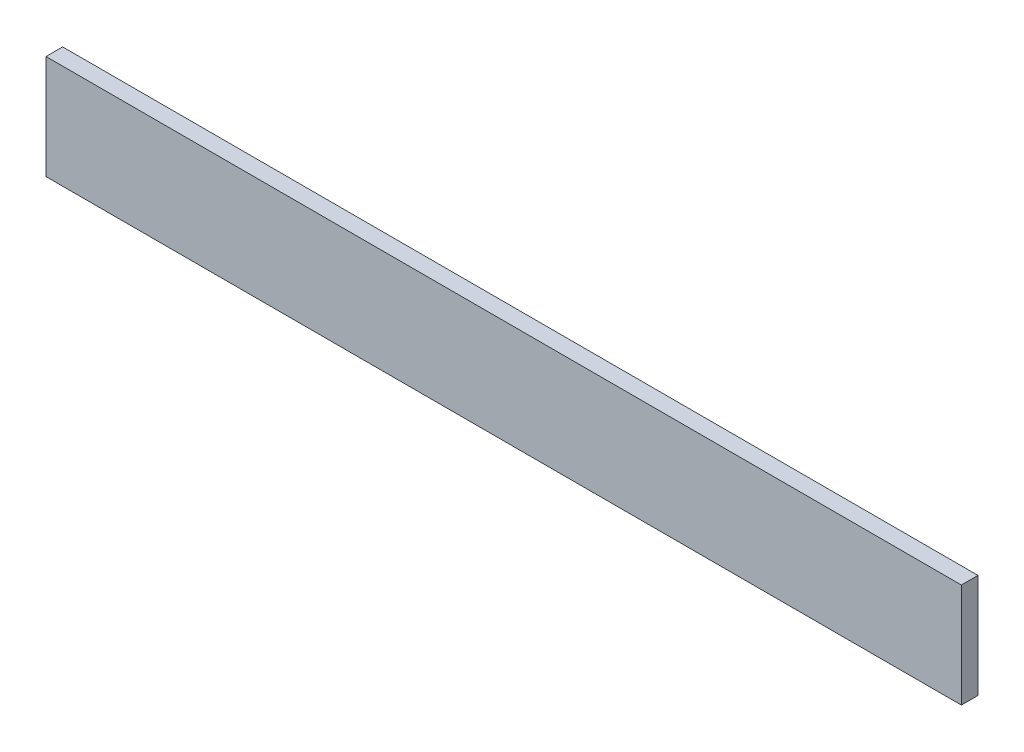
SolidWorks part; units mm, degrees
material "Cast Alloy Steel"
ref_plane "Front Plane" through (0, 0, 0) normal (0, 0, 1) x (1, 0, 0)
ref_plane "Top Plane" through (0, 0, 0) normal (0, 1, 0) x (1, 0, 0)
ref_plane "Right Plane" through (0, 0, 0) normal (1, 0, 0) x (0, 0, -1)
sketch "Sketch1" plane through (0, 0, 0) normal (0, 0, 1) x (1, 0, 0)
  line L1 (-110.9133, 31.0383) -> (109.0867, 31.0383)
  line L2 (-110.9133, 31.0383) -> (-110.9133, 6.0383)
  line L3 (-110.9133, 6.0383) -> (109.0867, 6.0383)
  line L4 (109.0867, 31.0383) -> (109.0867, 6.0383)
  dimension "D1" = 25
  dimension "D2" = 220
extrude "Boss-Extrude1" add sketch "Sketch1" along normal blind 4
